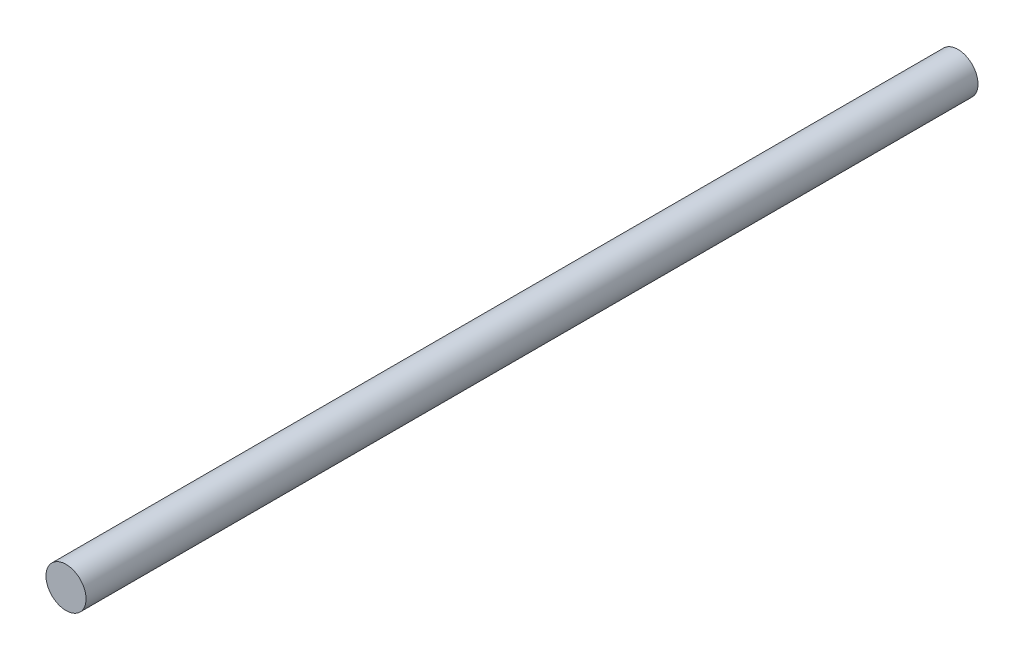
SolidWorks part; units mm, degrees
material "Nylon 101"
ref_plane "Front Plane" through (0, 0, 0) normal (0, 0, 1) x (1, 0, 0)
ref_plane "Top Plane" through (0, 0, 0) normal (0, 1, 0) x (1, 0, 0)
ref_plane "Right Plane" through (0, 0, 0) normal (1, 0, 0) x (0, 0, -1)
sketch "Sketch2" plane through (0, 0, 0) normal (0, 0, 1) x (1, 0, 0)
  circle A0 centre (0, 0) radius 5
  dimension "D1" = 10
extrude "Boss-Extrude1" add sketch "Sketch2" along normal blind 222.4
